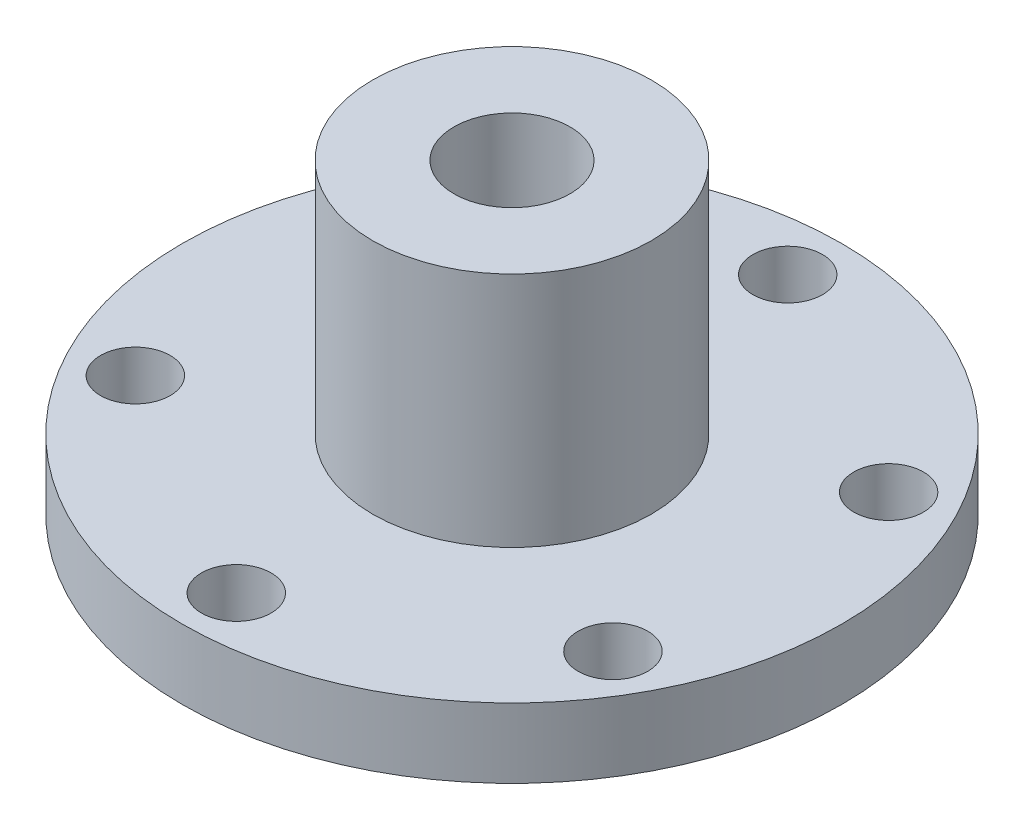
SolidWorks part; units mm, degrees
material "Alumina"
ref_plane "Front Plane" through (0, 0, 0) normal (0, 0, 1) x (1, 0, 0)
ref_plane "Top Plane" through (0, 0, 0) normal (0, 1, 0) x (1, 0, 0)
ref_plane "Right Plane" through (0, 0, 0) normal (1, 0, 0) x (0, 0, -1)
sketch "Sketch1" plane through (0, 0, 0) normal (0, 1, 0) x (1, 0, 0)
  circle A0 centre (0, 0) radius 28.4
  circle A1 centre (0, 0) radius 5
  circle A2 centre (0, 23.75) radius 3
  circle A3 centre (20.5681, 11.875) radius 3
  circle A4 centre (20.5681, -11.875) radius 3
  circle A5 centre (0, -23.75) radius 3
  circle A6 centre (-20.5681, -11.875) radius 3
  circle A7 centre (-20.5681, 11.875) radius 3
  point P18 (0, 0)
  dimension "D1" = 56.8
  dimension "D2" = 10
  dimension "D3" = 6
  dimension "D4" = 23.75
  dimension "D5" = 6
extrude "Boss-Extrude3" add sketch "Sketch1" along normal blind 6
sketch "Sketch5" plane through (0, 6, 0) normal (0, 1, 0) x (1, 0, 0)
  circle A0 centre (0, 0) radius 12
  circle A1 centre (0, 0) radius 5
  dimension "D1" = 24
extrude "Boss-Extrude4" add sketch "Sketch5" along normal blind 20.4
